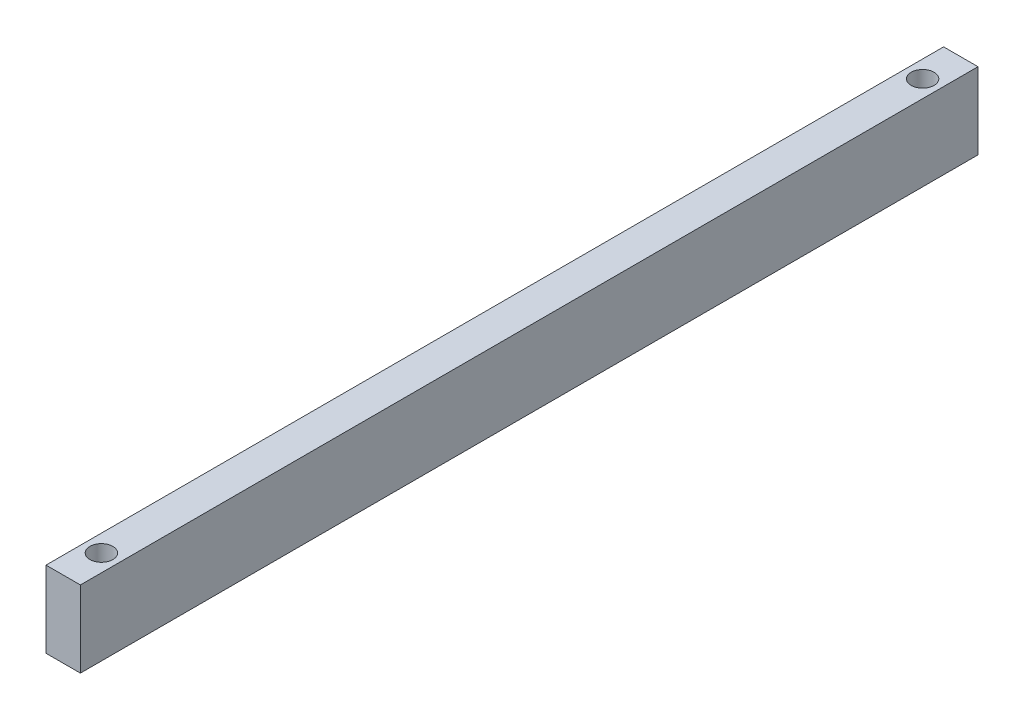
SolidWorks part; units mm, degrees
material "PA Type 6"
ref_plane "Front Plane" through (0, 0, 0) normal (0, 0, 1) x (1, 0, 0)
ref_plane "Top Plane" through (0, 0, 0) normal (0, 1, 0) x (1, 0, 0)
ref_plane "Right Plane" through (0, 0, 0) normal (1, 0, 0) x (0, 0, -1)
sketch "Sketch1" plane through (0, 0, 0) normal (0, 0, 1) x (1, 0, 0)
  line L1 (-4.5, -10) -> (4.5, -10)
  line L2 (-4.5, -10) -> (-4.5, 10)
  line L3 (-4.5, 10) -> (4.5, 10)
  line L4 (4.5, -10) -> (4.5, 10)
  line L5 (-4.5, -10) -> (4.5, 10) construction
  line L6 (-4.5, 10) -> (4.5, -10) construction
  point P0 (0, 0)
  dimension "D1" = 20
  dimension "D2" = 9
extrude "Boss-Extrude1" add sketch "Sketch1" along normal mid plane 235
sketch "Sketch3" plane through (0, 10, 0) normal (0, 1, 0) x (1, 0, 0)
  line L0 (0, -117.5) -> (0, -107.5) construction
  line L1 (4.5, -117.5) -> (-4.5, -117.5) construction
  circle A0 centre (0, -107.5) radius 3
  dimension "D1" = 6
  dimension "D2" = 10
extrude "Cut-Extrude2" cut sketch "Sketch3" against normal through all
mirror "Mirror2" about plane through (0, 0, 0) normal (0, 0, 1) of "Cut-Extrude2"
